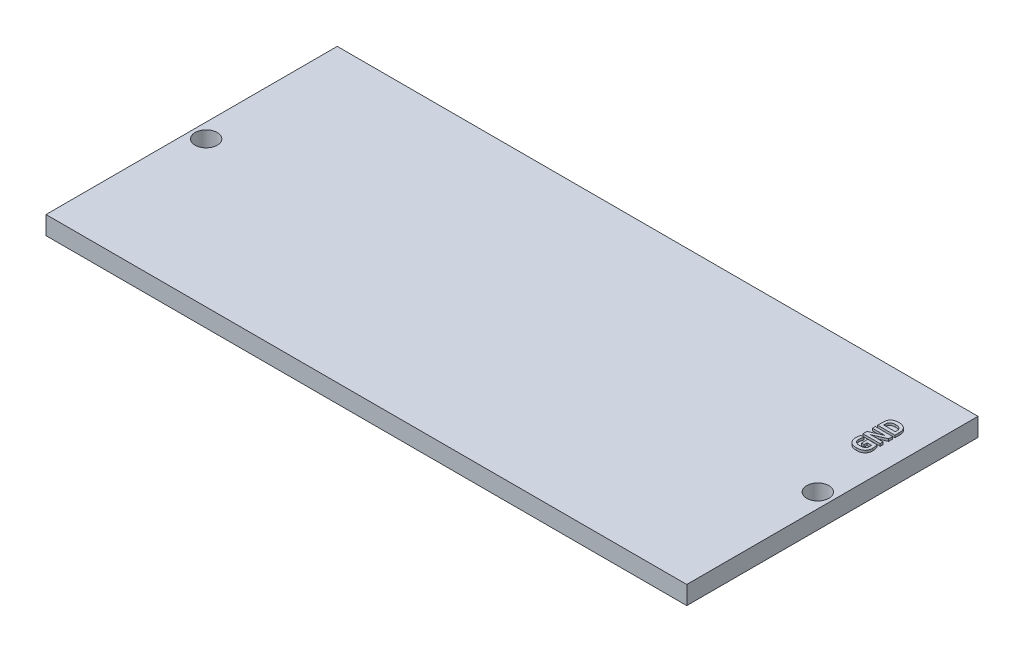
SolidWorks part; units mm, degrees
ref_plane "Front Plane" through (0, 0, 0) normal (0, 0, 1) x (1, 0, 0)
ref_plane "Top Plane" through (0, 0, 0) normal (0, 1, 0) x (1, 0, 0)
ref_plane "Right Plane" through (0, 0, 0) normal (1, 0, 0) x (0, 0, -1)
sketch "Sketch1" plane through (0, 0, 0) normal (0, 1, 0) x (1, 0, 0)
  line L1 (-13.97, 6.35) -> (13.97, 6.35)
  line L2 (-13.97, 6.35) -> (-13.97, -6.35)
  line L3 (-13.97, -6.35) -> (13.97, -6.35)
  line L4 (13.97, 6.35) -> (13.97, -6.35)
  line L5 (-13.97, 6.35) -> (13.97, -6.35) construction
  line L6 (-13.97, -6.35) -> (13.97, 6.35) construction
  point P0 (0, 0)
  dimension "D1" = 12.7
  dimension "D2" = 27.94
extrude "Boss-Extrude1" add sketch "Sketch1" along normal blind 0.8 contours L1 L4 L3 L2
sketch "Sketch2" plane through (0, 0.8, 0) normal (0, 1, 0) x (1, 0, 0)
  line L0 (13.97, 3.35) -> (12.97, 3.35) construction
  line L3 (13.97, 6.35) -> (13.97, -6.35) construction
  line L4 (-13.97, 6.35) -> (13.97, 6.35) construction
  line L5 (12.97, 2.35) -> (12.97, 4.35) construction
  text T0 "GND" font "Consolas" height 0.75
  dimension "D1" = 3
  dimension "D2" = 1
  dimension "D3" = 2
extrude "Boss-Extrude3" add sketch "Sketch2" along normal blind 0.1 separate body
sketch "Sketch3" plane through (0, 0.8, 0) normal (0, 1, 0) x (1, 0, 0)
  line L0 (-13.335, 0) -> (13.335, 0) construction
  circle A0 centre (-13.335, 0) radius 0.4826
  circle A1 centre (13.335, 0) radius 0.4826
  dimension "D2" = 0.9652
  dimension "D3" = 0.9652
extrude "Cut-Extrude1" cut sketch "Sketch3" against normal through all
